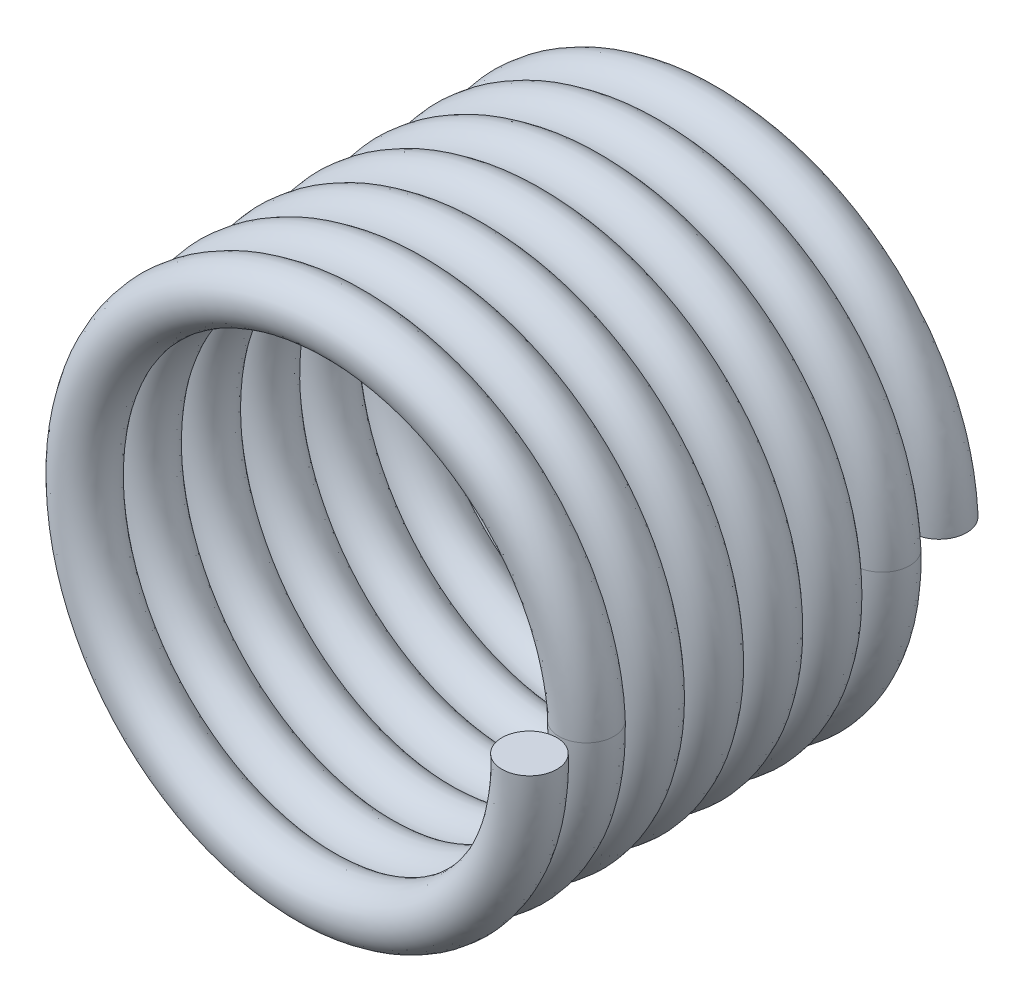
SolidWorks part; units mm, degrees
material "AISI 316 Stainless Steel Sheet (SS)"
ref_plane "Front" through (0, 0, 0) normal (0, 0, 1) x (1, 0, 0)
ref_plane "Top" through (0, 0, 0) normal (0, 1, 0) x (1, 0, 0)
ref_plane "Right" through (0, 0, 0) normal (1, 0, 0) x (0, 0, -1)
sketch "Sketch1" plane through (0, 0, 0) normal (0, 1, 0) x (1, 0, 0)
  line L0 (2.8448, 4.9276) -> (2.8448, 4.5974) construction
  line L1 (0, 0) -> (2.8448, 0) construction
  line L2 (0, 0) -> (0, 4.9276) construction
  line L3 (0, 4.9276) -> (2.8448, 4.9276) construction
  line L4 (2.8448, 4.5974) -> (2.8448, 4.572) construction
  line L5 (2.8448, 4.572) -> (2.8448, 3.9116) construction
  line L6 (2.8448, 3.9116) -> (2.8448, 1.016) construction
  line L7 (2.8448, 1.016) -> (2.8448, 0.3556) construction
  line L8 (2.8448, 0.3556) -> (2.8448, 0.3302) construction
  line L9 (2.8448, 0.3302) -> (2.8448, 0) construction
  line L10 (2.8448, 0) -> (3.175, 0) construction
  line L11 (2.8448, 0.6858) -> (3.175, 0.6858) construction
  line L12 (2.8448, 4.9276) -> (3.175, 4.9276) construction
  line L13 (2.8448, 4.9276) -> (2.8448, 5.2578) construction
  line L14 (2.8448, 0) -> (2.8448, -0.3302) construction
  circle A0 centre (2.8448, 4.9276) radius 0.3302 construction
  circle A1 centre (2.8448, 4.2418) radius 0.3302 construction
  circle A2 centre (2.8448, 0.6858) radius 0.3302
  circle A3 centre (2.8448, 0) radius 0.3302 construction
ref_plane "Plane1" through (0, 0, -0.6858) normal (0, 0, 1) x (-1, 0, 0)
ref_plane "Plane2" through (0, 0, -4.2418) normal (0, 0, 1) x (-1, 0, 0)
sketch "Sketch2" plane through (0, 0, -0.6858) normal (0, 0, 1) x (-1, 0, 0)
  circle A0 centre (0, 0) radius 3.175
curve "Helix1" pitch 0.7112 height 3.556 turns 5
sketch "Sketch3" plane through (0, 0, -0.6858) normal (0, 0, 1) x (-1, 0, 0)
  circle A0 centre (0, 0) radius 3.175 construction
  circle A1 centre (0, 0) radius 3.175
curve "Helix2" pitch 0.6858 height 0.6858 turns 1
sketch "Sketch4" plane through (0, 0, -4.2418) normal (0, 0, 1) x (-1, 0, 0)
  circle A0 centre (0, 0) radius 3.175 construction
  circle A1 centre (0, 0) radius 3.175
curve "Helix3" pitch 0.6858 height 0.6858 turns 1
sketch "Sketch5" plane through (0, 0, 0) normal (0, 1, 0) x (1, 0, 0)
  line L0 (2.8448, -0.3302) -> (2.8448, 5.2578) construction
  line L1 (2.5146, 0) -> (3.175, 0) construction
  circle A0 centre (2.8448, 0) radius 0.3302 construction
  circle A1 centre (2.8448, 0) radius 0.3302
curve "CompCurve1"
sweep "Sweep1" add profiles "Sketch5" path "CompCurve1"
equation "\"D3@Helix1\"=\"D3@Sketch1\""
equation "\"D3@Helix2\"=\"D4@Sketch1\""
equation "\"D3@Helix3\"=\"D4@Sketch1\""
